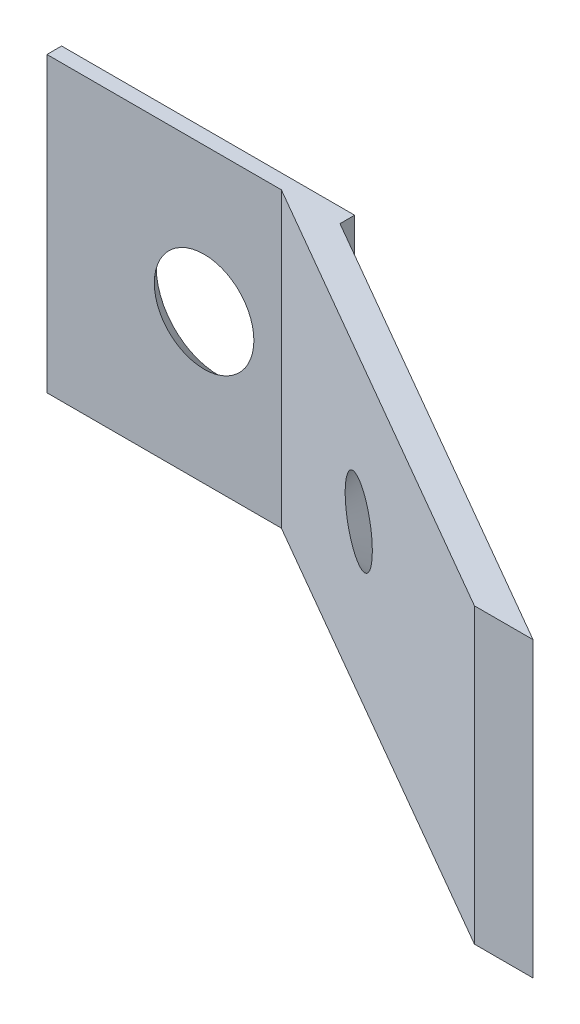
SolidWorks part; units mm, degrees
ref_plane "Front Plane" through (0, 0, 0) normal (0, 0, 1) x (1, 0, 0)
ref_plane "Top Plane" through (0, 0, 0) normal (0, 1, 0) x (1, 0, 0)
ref_plane "Right Plane" through (0, 0, 0) normal (1, 0, 0) x (0, 0, -1)
sketch "Sketch2" plane through (0, 0, 0) normal (0, 0, 1) x (1, 0, 0)
  line L0 (5, 0) -> (5, -10) construction
  line L1 (0, 0) -> (10, 0)
  line L2 (0, 0) -> (0, -10)
  line L3 (0, -10) -> (10, -10)
  line L4 (10, 0) -> (10, -10)
  line L5 (5, -10) -> (0, -5) construction
  line L6 (0, -5) -> (10.1099, -5) construction
  dimension "D1" = 10
  dimension "D2" = 10
extrude "Boss-Extrude1" add sketch "Sketch2" along normal blind 0.5
sketch "Sketch3" plane through (0, -10, 0) normal (0, -1, 0) x (1, 0, 0)
  line L0 (8, 0.5) -> (23.5885, 9.5)
  line L1 (0, 0.5) -> (10, 0.5) construction
  line L2 (23.5885, 9.5) -> (25.5885, 9.5)
  line L3 (25.5885, 9.5) -> (10, 0.5)
  line L4 (10, 0.5) -> (8, 0.5)
  dimension "D1" = 150
  dimension "D2" = 18
  dimension "D3" = 1
extrude "Boss-Extrude2" add sketch "Sketch3" against normal blind 10
sketch "Sketch6" plane through (0, 0, 0) normal (0, 0, -1) x (-1, 0, 0)
  point P0 (-5.3625, -4.9213)
hole_wizard "CSK for #1 Flat Head Socket Cap Screw1" positions "Sketch6" profile "Sketch7" countersink size "#1" standard "ANSI Inch" end condition through all
sketch "Sketch7" plane through (5.3625, -4.9213, 0) normal (1, 0, 0) x (0, 1, 0)
  line L0 (0, 0) -> (0, 9.5)
  line L1 (0, 9.5) -> (1.0287, 9.5)
  line L2 (1.0287, 9.5) -> (1.0287, 1.271)
  line L3 (1.0287, 1.271) -> (2.1336, 0)
  line L5 (2.1336, 0) -> (0, 0)
  line L6 (-1.0287, 1.271) -> (-2.1336, 0) construction
  line L11 (0, -6.35) -> (0, 107.95) construction
  dimension "Thru Hole Dia." = 2.0574
  dimension "Thru Hole Depth" = 9.5
  dimension "Near C'Sink Dia." = 4.2672
  dimension "Near C'Sink Angle" = 82
sketch "Sketch8" plane through (2.2835, 0, -3.9551) normal (0.5, 0, -0.866) x (-0.866, 0, -0.5)
  point P0 (-14.3915, -4.8794)
hole_wizard "CSK for #1 Flat Head Socket Cap Screw2" positions "Sketch8" profile "Sketch9" countersink size "#1" standard "ANSI Inch" end condition through all
sketch "Sketch9" plane through (14.7469, -4.8794, 3.2406) normal (0, 1, 0) x (-0.866, 0, -0.5)
  line L0 (0, 0) -> (0, 12.7942)
  line L1 (0, 12.7942) -> (1.0287, 12.7942)
  line L2 (1.0287, 12.7942) -> (1.0287, 1.271)
  line L3 (1.0287, 1.271) -> (2.1336, 0)
  line L5 (2.1336, 0) -> (0, 0)
  line L6 (-1.0287, 1.271) -> (-2.1336, 0) construction
  line L11 (0, -6.35) -> (0, 107.95) construction
  dimension "Thru Hole Dia." = 2.0574
  dimension "Thru Hole Depth" = 12.7942
  dimension "Near C'Sink Dia." = 4.2672
  dimension "Near C'Sink Angle" = 82
